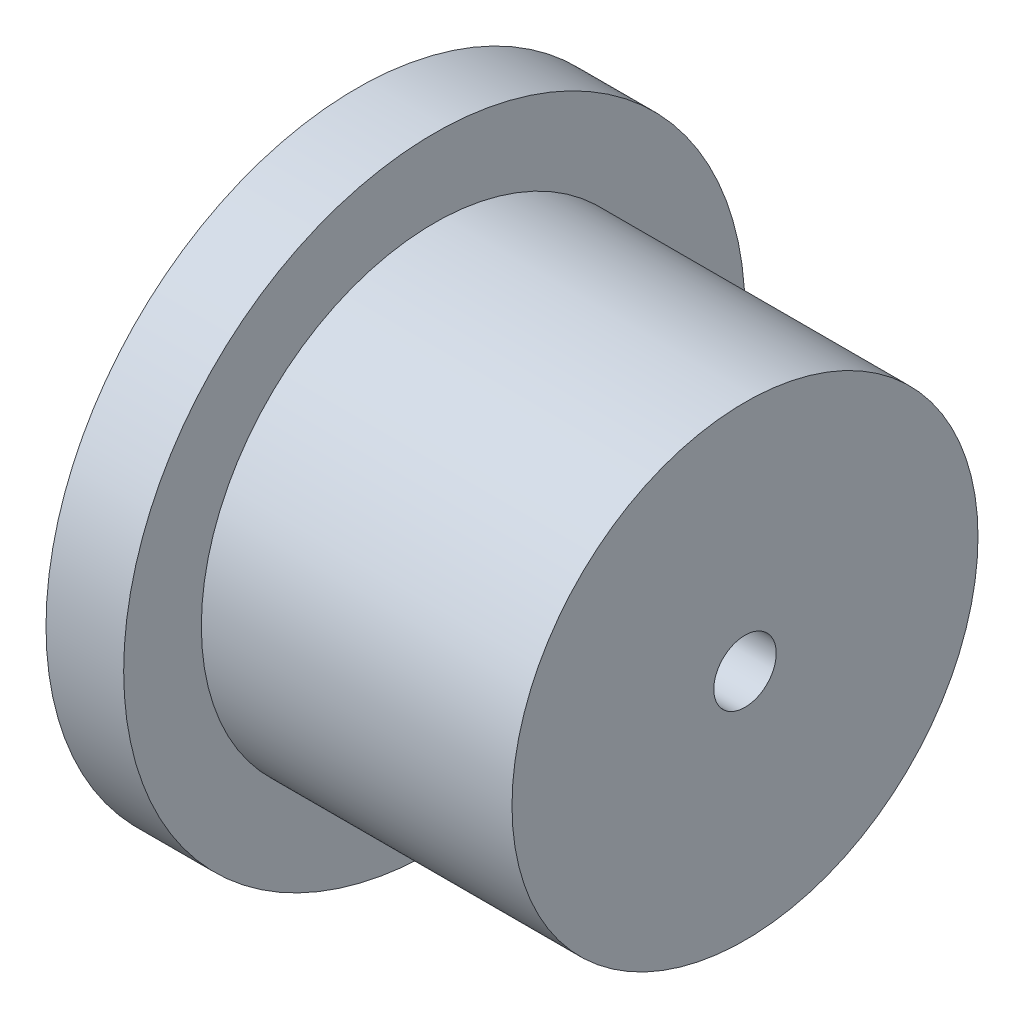
SolidWorks part; units mm, degrees
material "Aluminum Bronze"
ref_plane "Front" through (0, 0, 0) normal (0, 0, 1) x (1, 0, 0)
ref_plane "Top" through (0, 0, 0) normal (0, 1, 0) x (1, 0, 0)
ref_plane "Right" through (0, 0, 0) normal (1, 0, 0) x (0, 0, -1)
sketch "Sketch1" plane through (0, 0, 0) normal (0, 0, 1) x (1, 0, 0)
  line L0 (0, 39.4433) -> (0, -31.7844) construction
  line L1 (-45.9652, 0) -> (29.1474, 0) construction
  line L2 (0, 0) -> (0, -19.05)
  line L3 (0, -19.05) -> (-25.4, -19.05)
  line L4 (-25.4, -19.05) -> (-25.4, -25.4)
  line L5 (-25.4, -25.4) -> (-31.75, -25.4)
  line L6 (-31.75, -25.4) -> (-31.75, 0)
  line L7 (-31.75, 0) -> (0, 0)
  dimension "D1" = 38.1
  dimension "D2" = 50.8
  dimension "D3" = 31.75
  dimension "D4" = 6.35
revolve "Revolve1" add sketch "Sketch1" angle 360 about L1
hole_wizard "1/4-20 Tapped Hole1" positions "Sketch4" profile "Sketch5" tap size "1/4-20" standard "ANSI Inch" end condition through all
sketch "Sketch4" plane through (-31.75, 0, 0) normal (-1, 0, 0) x (0, 0, 1)
  point P0 (0, 0)
sketch "Sketch5" plane through (-31.75, 0, 0) normal (0, 1, 0) x (0, 0, 1)
  line L0 (0, 0) -> (0, 31.75)
  line L1 (0, 31.75) -> (2.5527, 31.75)
  line L2 (2.5527, 31.75) -> (2.5527, 1.055)
  line L3 (2.5527, 1.055) -> (3.81, 0)
  line L5 (3.81, 0) -> (0, 0)
  line L6 (-2.5527, 1.055) -> (-3.81, 0) construction
  line L11 (0, -6.35) -> (0, 107.95) construction
  dimension "Thru Tap Drill Dia." = 5.1054
  dimension "Thru Tap Drill Depth" = 31.75
  dimension "Near C'Sink Dia." = 7.62
  dimension "Near C'Sink Angle" = 100
cosmetic thread "Hole Thread1" parameters "D2"=6.35
